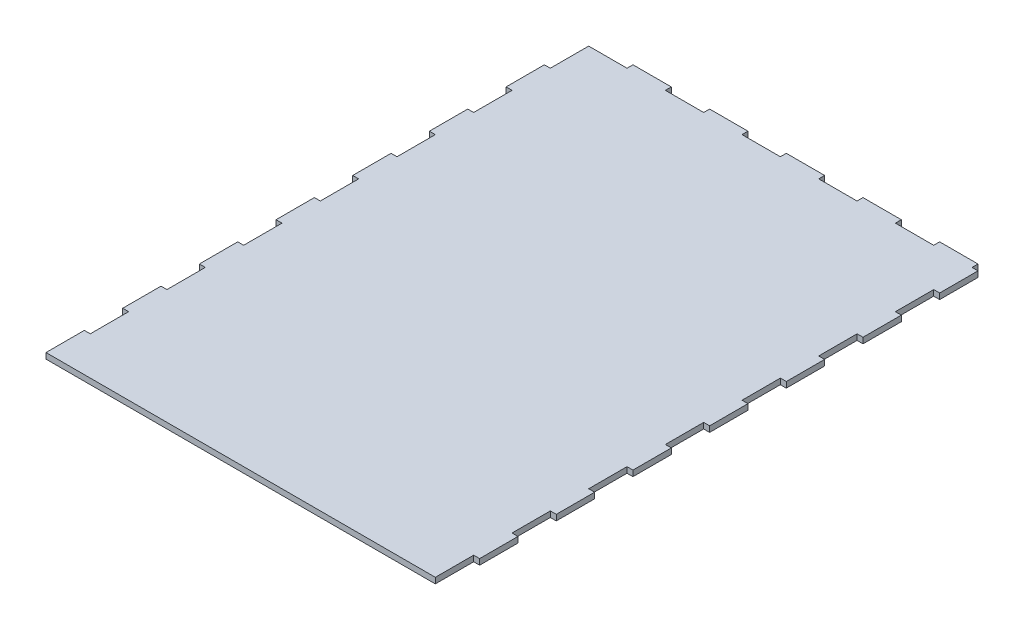
SolidWorks part; units mm, degrees
material "Acrílico (Impacto medio-alto)"
ref_plane "Alzado" through (0, 0, 0) normal (0, 0, 1) x (1, 0, 0)
ref_plane "Planta" through (0, 0, 0) normal (0, 1, 0) x (1, 0, 0)
ref_plane "Vista lateral" through (0, 0, 0) normal (1, 0, 0) x (0, 0, -1)
sketch "Croquis1" plane through (0, 0, 0) normal (0, 1, 0) x (1, 0, 0)
  line L1 (0, 0) -> (200, 0)
  line L2 (0, 0) -> (0, 280) construction
  line L3 (0, 280) -> (200, 280) construction
  line L4 (200, 0) -> (200, 280) construction
  line L20 (200, 280) -> (203.1, 280)
  line L21 (203.1, 280) -> (203.1, 260)
  line L22 (203.1, 260) -> (200, 260)
  line L23 (200, 260) -> (200, 240)
  line L24 (200, 240) -> (203.1, 240)
  line L25 (203.1, 240) -> (203.1, 220)
  line L26 (203.1, 220) -> (200, 220)
  line L27 (200, 220) -> (200, 200)
  line L28 (200, 200) -> (203.1, 200)
  line L29 (203.1, 200) -> (203.1, 180)
  line L30 (203.1, 180) -> (200, 180)
  line L31 (200, 180) -> (200, 160)
  line L32 (200, 160) -> (203.1, 160)
  line L33 (203.1, 160) -> (203.1, 140)
  line L34 (203.1, 140) -> (200, 140)
  line L35 (200, 140) -> (200, 120)
  line L36 (200, 120) -> (203.1, 120)
  line L37 (203.1, 120) -> (203.1, 100)
  line L38 (203.1, 100) -> (200, 100)
  line L39 (200, 100) -> (200, 80)
  line L40 (200, 80) -> (203.1, 80)
  line L41 (203.1, 80) -> (203.1, 60)
  line L42 (203.1, 60) -> (200, 60)
  line L43 (200, 60) -> (200, 40)
  line L44 (200, 40) -> (203.1, 40)
  line L45 (203.1, 40) -> (203.1, 20)
  line L46 (203.1, 20) -> (200, 20)
  line L47 (200, 20) -> (200, 0)
  line L48 (0, 280) -> (0, 260)
  line L49 (0, 260) -> (-3.1, 260)
  line L50 (-3.1, 260) -> (-3.1, 240)
  line L51 (-3.1, 240) -> (0, 240)
  line L52 (0, 240) -> (0, 220)
  line L53 (0, 220) -> (-3.1, 220)
  line L54 (-3.1, 220) -> (-3.1, 200)
  line L55 (-3.1, 200) -> (0, 200)
  line L56 (0, 200) -> (0, 180)
  line L57 (0, 180) -> (-3.1, 180)
  line L58 (-3.1, 180) -> (-3.1, 160)
  line L59 (-3.1, 160) -> (0, 160)
  line L60 (0, 160) -> (0, 140)
  line L61 (0, 140) -> (-3.1, 140)
  line L62 (-3.1, 140) -> (-3.1, 120)
  line L63 (-3.1, 120) -> (0, 120)
  line L64 (0, 120) -> (0, 100)
  line L65 (0, 100) -> (-3.1, 100)
  line L66 (-3.1, 100) -> (-3.1, 80)
  line L67 (-3.1, 80) -> (0, 80)
  line L68 (0, 80) -> (0, 60)
  line L69 (0, 60) -> (-3.1, 60)
  line L70 (-3.1, 60) -> (-3.1, 40)
  line L71 (-3.1, 40) -> (0, 40)
  line L72 (0, 40) -> (0, 20)
  line L73 (0, 20) -> (-3.1, 20)
  line L74 (-3.1, 20) -> (-3.1, 0)
  line L75 (-3.1, 0) -> (0, 0)
  line L76 (0, 280) -> (20, 280)
  line L77 (20, 280) -> (20, 283.1)
  line L78 (20, 283.1) -> (40, 283.1)
  line L79 (40, 283.1) -> (40, 280)
  line L80 (40, 280) -> (60, 280)
  line L81 (60, 280) -> (60, 283.1)
  line L82 (60, 283.1) -> (80, 283.1)
  line L83 (80, 283.1) -> (80, 280)
  line L84 (80, 280) -> (100, 280)
  line L85 (100, 280) -> (100, 283.1)
  line L86 (100, 283.1) -> (120, 283.1)
  line L87 (120, 283.1) -> (120, 280)
  line L88 (120, 280) -> (140, 280)
  line L89 (140, 280) -> (140, 283.1)
  line L90 (140, 283.1) -> (160, 283.1)
  line L91 (160, 283.1) -> (160, 280)
  line L92 (160, 280) -> (180, 280)
  line L93 (180, 280) -> (180, 283.1)
  line L94 (180, 283.1) -> (200, 283.1)
  line L95 (200, 283.1) -> (200, 280)
  dimension "D2" = 7
  dimension "D3" = 7
extrude "Saliente-Extruir1" add sketch "Croquis1" along normal blind 3
